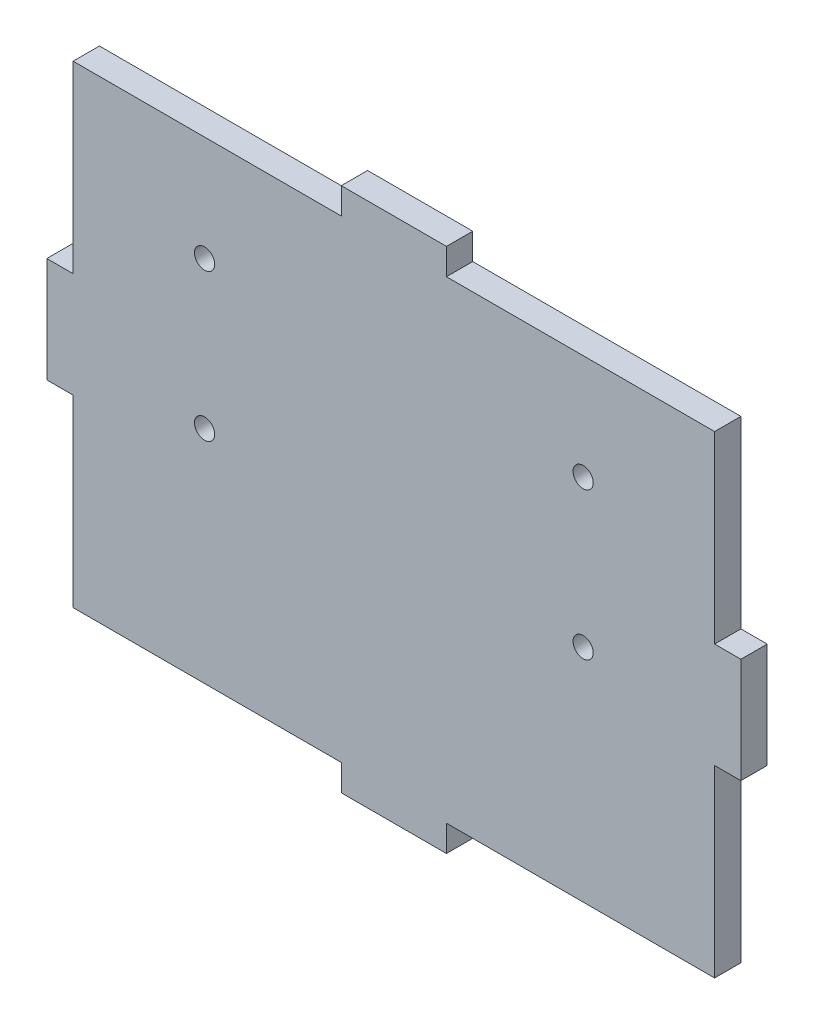
SolidWorks part; units mm, degrees
material "Acrylic (Medium-high impact)"
ref_plane "Front Plane" through (0, 0, 0) normal (0, 0, 1) x (1, 0, 0)
ref_plane "Top Plane" through (0, 0, 0) normal (0, 1, 0) x (1, 0, 0)
ref_plane "Right Plane" through (0, 0, 0) normal (1, 0, 0) x (0, 0, -1)
sketch "Sketch1" plane through (0, 0, 0) normal (0, 0, 1) x (1, 0, 0)
  line L0 (-38.735, 6.35) -> (-41.91, 6.35)
  line L1 (-38.735, -28.575) -> (-6.35, -28.575)
  line L2 (-38.735, -28.575) -> (-38.735, -6.35)
  line L3 (-38.735, 28.575) -> (-6.35, 28.575)
  line L4 (38.735, -28.575) -> (38.735, -6.35)
  line L5 (-38.735, -28.575) -> (38.735, 28.575) construction
  line L6 (-38.735, 28.575) -> (38.735, -28.575) construction
  line L7 (-41.91, 6.35) -> (-41.91, -6.35)
  line L8 (-41.91, -6.35) -> (-38.735, -6.35)
  line L9 (6.35, 28.575) -> (38.735, 28.575)
  line L10 (-6.35, 28.575) -> (-6.35, 31.75)
  line L11 (-6.35, 31.75) -> (6.35, 31.75)
  line L12 (6.35, 31.75) -> (6.35, 28.575)
  line L13 (38.735, 6.35) -> (38.735, 28.575)
  line L14 (38.735, 6.35) -> (41.91, 6.35)
  line L15 (41.91, 6.35) -> (41.91, -6.35)
  line L16 (41.91, -6.35) -> (38.735, -6.35)
  line L17 (-6.35, -28.575) -> (-6.35, -31.75)
  line L18 (-6.35, -31.75) -> (6.35, -31.75)
  line L19 (6.35, -31.75) -> (6.35, -28.575)
  line L20 (6.35, -28.575) -> (38.735, -28.575)
  line L21 (-38.735, 6.35) -> (-38.735, 28.575)
  point P0 (0, 0)
  dimension "D1" = 77.47
  dimension "D2" = 57.15
  dimension "D3" = 3.175
  dimension "D4" = 12.7
extrude "Boss-Extrude1" add sketch "Sketch1" along normal blind 3.175
sketch "Sketch2" plane through (0, 0, 3.175) normal (0, 0, 1) x (1, 0, 0)
  line L0 (0, 0) -> (0, 15.875) construction
  line L1 (0, 15.875) -> (0, 31.75) construction
  line L2 (6.35, 31.75) -> (-6.35, 31.75) construction
  line L3 (38.735, 28.575) -> (6.35, 28.575) construction
  line L4 (0, 15.875) -> (-22.86, 15.875) construction
  line L5 (-22.86, 15.875) -> (-22.86, -1.905) construction
  line L6 (-22.86, -1.905) -> (22.86, -1.905) construction
  line L7 (22.86, -1.905) -> (22.86, 15.875) construction
  line L8 (22.86, 15.875) -> (0, 15.875) construction
  circle A0 centre (-22.86, 15.875) radius 1.2192
  circle A1 centre (22.86, 15.875) radius 1.2192
  circle A2 centre (22.86, -1.905) radius 1.2192
  circle A3 centre (-22.86, -1.905) radius 1.2192
  dimension "D5" = 2.4384
  dimension "D1" = 12.7
  dimension "D2" = 22.86
  dimension "D3" = 22.86
  dimension "D4" = 17.78
extrude "Cut-Extrude1" cut sketch "Sketch2" against normal through all
